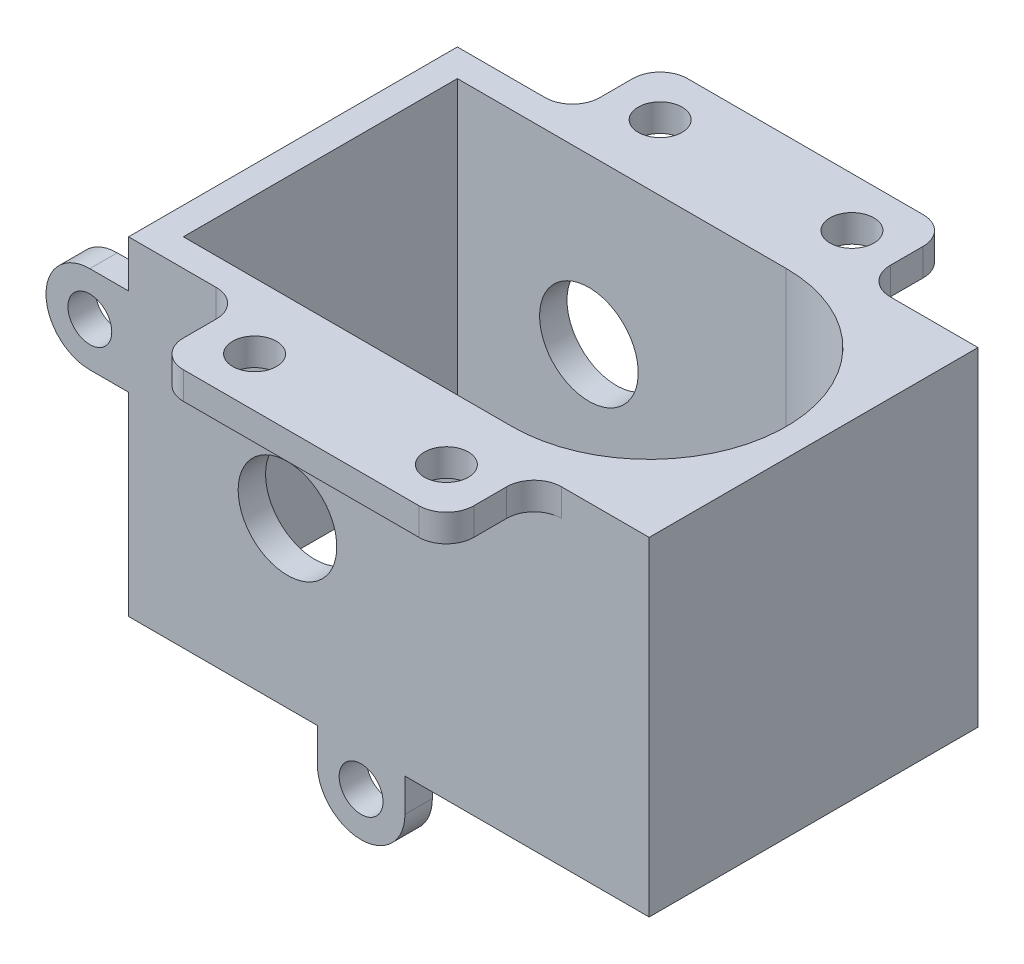
SolidWorks part; units mm, degrees
ref_plane "Alzado" through (0, 0, 0) normal (0, 0, 1) x (1, 0, 0)
ref_plane "Planta" through (0, 0, 0) normal (0, 1, 0) x (1, 0, 0)
ref_plane "Vista lateral" through (0, 0, 0) normal (1, 0, 0) x (0, 0, -1)
sketch "Croquis1" plane through (0, 0, 0) normal (0, 1, 0) x (1, 0, 0)
  line L1 (-15, -15) -> (15, -15)
  line L2 (-15, -15) -> (-15, 15)
  line L3 (-15, 15) -> (15, 15)
  line L4 (15, -15) -> (15, 15)
  line L5 (-15, -15) -> (15, 15) construction
  line L6 (-15, 15) -> (15, -15) construction
  point P0 (0, 0)
  dimension "D1" = 30
  dimension "D2" = 30
extrude "Saliente-Extruir1" add sketch "Croquis1" along normal blind 30
sketch "Croquis2" plane through (0, 30, 0) normal (0, 1, 0) x (1, 0, 0)
  circle A0 centre (0, 0) radius 12.5
  dimension "D1" = 25
extrude "Cortar-Extruir1" cut sketch "Croquis2" against normal blind 30
sketch "Croquis4" plane through (-15, 0, 0) normal (-1, 0, 0) x (0, 0, 1)
  line L1 (-15, 0) -> (15, 0)
  line L2 (-15, 0) -> (-15, 30)
  line L3 (-15, 30) -> (15, 30)
  line L4 (15, 0) -> (15, 30)
extrude "Saliente-Extruir5" add sketch "Croquis4" along normal blind 17.5
sketch "Croquis6" plane through (0, 30, 0) normal (0, 1, 0) x (1, 0, 0)
  line L0 (0, 12.5) -> (0, -12.5)
  line L1 (0, 12.5) -> (-30, 12.5)
  line L2 (0, -12.5) -> (-30, -12.5)
  line L3 (-30, 12.5) -> (-30, -12.5)
  line L4 (15, 15) -> (-32.5, 15) construction
  line L5 (-32.5, -15) -> (-32.5, 15) construction
  circle A0 centre (0, 0) radius 12.5 construction
  dimension "D1" = 2.5
  dimension "D2" = 2.5
extrude "Cortar-Extruir3" cut sketch "Croquis6" against normal blind 37.5
sketch "Croquis7" plane through (0, 0, -15) normal (0, 0, -1) x (-1, 0, 0)
  line L0 (-15, 30) -> (-15, 0) construction
  circle A0 centre (18, 15) radius 4.5
  dimension "D1" = 9
  dimension "D2" = 33
extrude "Cortar-Extruir5" cut sketch "Croquis7" against normal blind 37.5
sketch "Croquis8" plane through (0, 0, 15) normal (0, 0, 1) x (1, 0, 0)
  line L0 (-36.0312, 25.7175) -> (-32.5, 25.7175)
  line L1 (-32.5, 0) -> (-32.5, 30) construction
  line L2 (-32.5, 25.7175) -> (-32.5, 17.7175)
  line L11 (-32.5, 17.7175) -> (-36.0312, 17.7175)
  line L12 (-15.2825, -3.0312) -> (-15.2825, 0)
  line L13 (-32.5, 0) -> (15, 0) construction
  line L14 (-15.2825, 0) -> (-7.2825, 0)
  line L15 (-7.2825, 0) -> (-7.2825, -3.0312)
  circle A0 centre (-36.0312, 21.7175) radius 2
  circle A1 centre (-11.2825, -3.0312) radius 2
  arc A4 (-36.0312, 25.7175) -> (-36.0312, 17.7175) centre (-36.0312, 21.7175) ccw
  arc A5 (-7.2825, -3.0312) -> (-15.2825, -3.0312) centre (-11.2825, -3.0312) cw
  dimension "D4" = 4
  dimension "D5" = 4
extrude "Saliente-Extruir6" add sketch "Croquis8" against normal blind 2.5
sketch "Croquis9" plane through (0, 30, 0) normal (0, 1, 0) x (1, 0, 0)
  line L0 (15, -15) -> (15, 15) construction
  line L1 (-32.5, -15) -> (-32.5, 15) construction
  line L2 (15, 15) -> (-32.5, 15) construction
  line L3 (-22, 15) -> (4.5, 15)
  line L4 (-22, 15) -> (-22, 23)
  line L5 (-22, 23) -> (4.5, 23)
  line L6 (4.5, 15) -> (4.5, 23)
  line L7 (-32.5, -15) -> (15, -15) construction
  line L8 (-22, -15) -> (4.5, -15)
  line L9 (-22, -15) -> (-22, -23)
  line L10 (-22, -23) -> (4.5, -23)
  line L11 (4.5, -15) -> (4.5, -23)
  circle A0 centre (0, 18.5) radius 2
  circle A1 centre (0, -18.5) radius 2
  circle A2 centre (-17.5, 18.5) radius 2
  circle A3 centre (-17.5, -18.5) radius 2
  point P6 (15, 0)
  dimension "D1" = 4
  dimension "D2" = 4
  dimension "D6" = 4
  dimension "D8" = 4
  dimension "D15" = 4.5
  dimension "D3" = 37
  dimension "D4" = 18.5
  dimension "D5" = 15
  dimension "D7" = 15
  dimension "D9" = 4.5
  dimension "D10" = 37
  dimension "D11" = 37
  dimension "D12" = 15
  dimension "D13" = 17.5
  dimension "D14" = 15
  dimension "D16" = 4.5
  dimension "D17" = 4.5
  dimension "D18" = 4.5
  dimension "D19" = 4.5
extrude "Saliente-Extruir7" add sketch "Croquis9" against normal blind 2.5
fillet "Redondeo1" radius 2.5 8 edges at (4.5, 28.75, 15) (-22, 28.75, 15) (-22, 28.75, -15) (4.5, 28.75, -15) (-22, 28.75, -23) (4.5, 28.75, -23) (-22, 28.75, 23) (4.5, 28.75, 23)
